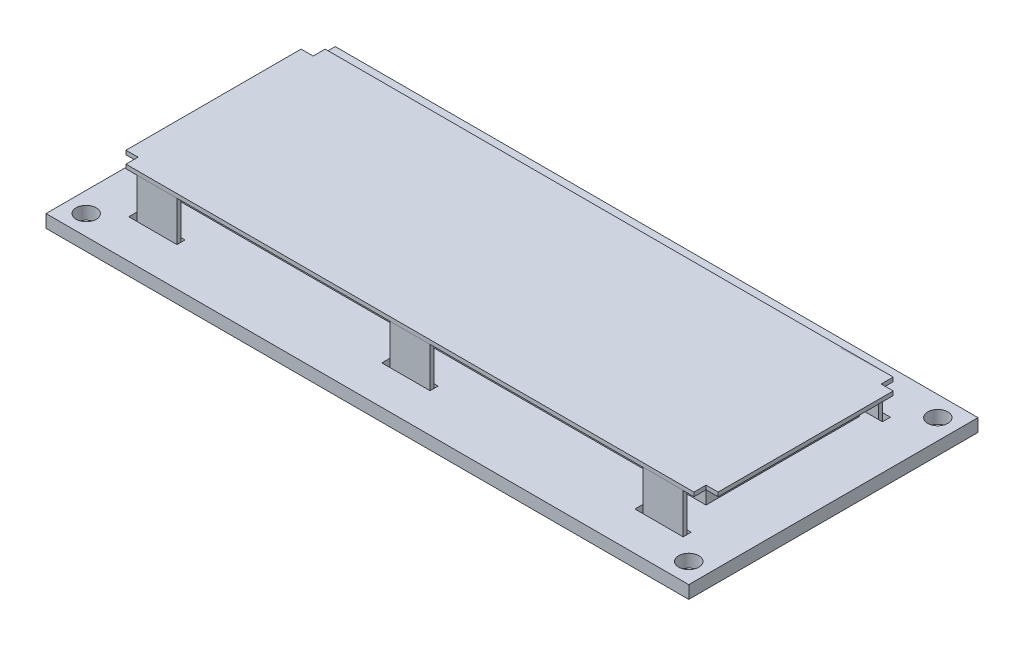
SolidWorks part; units mm, degrees
ref_plane "Ebene vorne" through (0, 0, 0) normal (0, 0, 1) x (1, 0, 0)
ref_plane "Ebene oben" through (0, 0, 0) normal (0, 1, 0) x (1, 0, 0)
ref_plane "Ebene rechts" through (0, 0, 0) normal (1, 0, 0) x (0, 0, -1)
sketch "Skizze1" plane through (0, 0, 0) normal (1, 0, 0) x (0, 0, -1)
  line L0 (0, 0) -> (36, 0)
  line L1 (0, 0) -> (0, -1.6)
  line L2 (0, -1.6) -> (36, -1.6)
  line L3 (36, -1.6) -> (36, 0)
  dimension "D1" = 36
  dimension "D2" = 1.6
extrude "Linear austragen1" add sketch "Skizze1" along normal blind 40
hole_wizard "Ø2.5 (2.5) Durchmesser Bohrung1" positions "3D-Skizze1" profile "Skizze3" hole size "Ø2.5" standard "Ansi Metrisch" end condition through all
sketch3d "3D-Skizze1"
  line L0 (40, 0, -36) -> (40, 0, 0) construction
  line L1 (40, 0, -36) -> (0, 0, -36) construction
  line L2 (40, 0, 0) -> (0, 0, 0) construction
  point P0 (37.5, 0, -2.5)
  point P2 (37.5, 0, -33.5)
  dimension "D1" = 2.5
  dimension "D2" = 2.5
  dimension "D3" = 2.5
  dimension "D4" = 2.5
sketch "Skizze3" plane through (37.5, 0, -2.5) normal (1, 0, 0) x (0, 0, 1)
  line L0 (0, 0) -> (0, 1.6)
  line L1 (0, 1.6) -> (1.25, 1.6)
  line L2 (1.25, 1.6) -> (1.25, 0)
  line L5 (1.25, 0) -> (0, 0)
  line L11 (0, -6.35) -> (0, 107.95) construction
  dimension "Bohrerdurchmesser" = 2.5
  dimension "Bohrungstiefe" = 1.6
sketch "Skizze7" plane through (0, 0, 0) normal (0, 1, 0) x (1, 0, 0)
  line L0 (0, 0) -> (0, 36) construction
  line L1 (0, 30.6) -> (3, 30.6)
  line L2 (0, 30.6) -> (0, 29.6)
  line L3 (0, 29.6) -> (3, 29.6)
  line L4 (3, 30.6) -> (3, 29.6)
  line L5 (28.5, 30.6) -> (34.5, 30.6)
  line L6 (28.5, 30.6) -> (28.5, 29.6)
  line L7 (28.5, 29.6) -> (34.5, 29.6)
  line L8 (34.5, 30.6) -> (34.5, 29.6)
  line L9 (40, 36) -> (0, 36) construction
  line L10 (40, 36) -> (40, 0) construction
  line L11 (40, 36) -> (0, 36) construction
  line L13 (34.5, 4.8) -> (34.5, 5.8)
  line L14 (28.5, 5.8) -> (34.5, 5.8)
  line L15 (28.5, 4.8) -> (28.5, 5.8)
  line L16 (28.5, 4.8) -> (34.5, 4.8)
  line L17 (3, 4.8) -> (3, 5.8)
  line L18 (0, 5.8) -> (3, 5.8)
  line L19 (0, 4.8) -> (0, 5.8)
  line L20 (0, 4.8) -> (3, 4.8)
  dimension "D1" = 1
  dimension "D2" = 5.4
  dimension "D3" = 3
  dimension "D4" = 6
  dimension "D5" = 5.5
  dimension "D6" = 25.8
extrude "Linear austragen4" cut sketch "Skizze7" against normal through all
mirror "Spiegeln1" about plane through (0, -1.6, 0) normal (1, 0, 0) of "Linear austragen4", "Linear austragen1", "Ø2.5 (2.5) Durchmesser Bohrung1"
sketch "Skizze5" plane through (0, 0, 0) normal (0, 1, 0) x (1, 0, 0)
  line L0 (0, 30.1) -> (35.35, 30.1)
  line L1 (35.35, 30.1) -> (35.35, 28.6)
  line L2 (35.35, 28.6) -> (36.85, 28.6)
  line L3 (36.85, 28.6) -> (36.85, 6.8)
  line L4 (36.85, 6.8) -> (35.35, 6.8)
  line L5 (35.35, 6.8) -> (35.35, 5.3)
  line L6 (35.35, 5.3) -> (0, 5.3)
  line L8 (0, 36) -> (0, 0) construction
  line L9 (40, 36) -> (-40, 36) construction
  line L10 (40, 36) -> (40, 0) construction
  line L11 (0, 5.3) -> (0, 30.1)
  dimension "D1" = 24.8
  dimension "D2" = 3.15
  dimension "D3" = 1.5
  dimension "D4" = 5.9
extrude "Linear austragen2" add sketch "Skizze5" along normal blind 0.5 from offset 4.5 separate body
mirror "Spiegeln8" about plane through (0, 5, -5.3) normal (1, 0, 0) of "Linear austragen2"
sketch "Skizze6" plane through (0, 5, 0) normal (0, 1, 0) x (1, 0, 0)
  line L0 (-35.35, 5.3) -> (35.35, 5.3) construction
  line L1 (35.35, 30.1) -> (-35.35, 30.1) construction
  line L2 (2.5, 30.1) -> (0, 30.1)
  line L3 (0, 30.1) -> (0, 36) construction
  line L4 (-35.35, 5.3) -> (35.35, 5.3) construction
  line L5 (0, 5.3) -> (2.5, 5.3)
  line L6 (40, 36) -> (-40, 36) construction
  line L7 (0, 30.1) -> (-2.5, 30.1)
  line L8 (0, 30.1) -> (0, 5.3) construction
  line L9 (0, 5.3) -> (-2.5, 5.3)
  line L10 (34, 30.1) -> (31.5, 30.1)
  line L12 (-2.5, 30.1) -> (-2.5, 29.6)
  line L13 (-2.5, 29.6) -> (2.5, 29.6)
  line L14 (2.5, 29.6) -> (2.5, 30.1)
  line L15 (31.5, 5.3) -> (34, 5.3)
  line L16 (31.5, 30.1) -> (29, 30.1)
  line L17 (-2.5, 5.3) -> (-2.5, 5.8)
  line L18 (-2.5, 5.8) -> (2.5, 5.8)
  line L19 (2.5, 5.8) -> (2.5, 5.3)
  line L20 (31.5, 5.3) -> (29, 5.3)
  line L21 (29, 30.1) -> (29, 29.6)
  line L22 (29, 29.6) -> (34, 29.6)
  line L23 (34, 29.6) -> (34, 30.1)
  line L24 (29, 5.3) -> (29, 5.8)
  line L25 (29, 5.8) -> (34, 5.8)
  line L26 (34, 5.8) -> (34, 5.3)
  line L27 (31.5, 30.1) -> (31.5, 5.3) construction
  line L28 (-29, 30.1) -> (-31.5, 30.1)
  line L29 (-31.5, 5.3) -> (-29, 5.3)
  line L30 (-31.5, 30.1) -> (-34, 30.1)
  line L31 (-31.5, 5.3) -> (-34, 5.3)
  line L32 (-34, 30.1) -> (-34, 29.6)
  line L33 (-34, 29.6) -> (-29, 29.6)
  line L34 (-29, 29.6) -> (-29, 30.1)
  line L35 (-34, 5.3) -> (-34, 5.8)
  line L36 (-34, 5.8) -> (-29, 5.8)
  line L37 (-29, 5.8) -> (-29, 5.3)
  line L38 (-31.5, 30.1) -> (-31.5, 36) construction
  line L39 (-31.5, 30.1) -> (-31.5, 5.3) construction
  dimension "D1" = 0.5
  dimension "D2" = 5
extrude "Linear austragen3" add sketch "Skizze6" against normal blind 11 separate body
sketch "Skizze8" plane through (0, 4.5, 0) normal (0, -1, 0) x (1, 0, 0)
  line L0 (-34, -27.25) -> (-36.85, -27.25) construction
  line L1 (-34, -27.25) -> (34, -27.25)
  line L2 (-34, -27.25) -> (-34, -8.15)
  line L3 (-34, -8.15) -> (34, -8.15)
  line L4 (34, -27.25) -> (34, -8.15)
  line L5 (-36.85, -6.8) -> (-36.85, -28.6) construction
  line L6 (-36.85, -27.25) -> (-34, -27.25) construction
  line L7 (-34, -27.25) -> (-34, -30.1) construction
  line L8 (34, -8.15) -> (34, -5.3) construction
  line L9 (29, -5.3) -> (34, -5.3) construction
  line L10 (34, -8.15) -> (36.85, -8.15) construction
  line L11 (36.85, -6.8) -> (36.85, -28.6) construction
extrude "Linear austragen5" add sketch "Skizze8" along normal blind 3
hole_wizard "Ø1.0 (1) Durchmesser Bohrung1" positions "3D-Skizze2" profile "Skizze9" hole size "Ø1.0" standard "Ansi Metrisch"
sketch3d "3D-Skizze2"
  line L0 (-40, 0, -36) -> (-40, 0, 0) construction
  line L1 (40, 0, -36) -> (-40, 0, -36) construction
  point P0 (-32, 0, -33.5)
  dimension "D1" = 8
  dimension "D2" = 2.5
sketch "Skizze9" plane through (-32, 0, -33.5) normal (1, 0, 0) x (0, 0, 1)
  line L0 (0, 0) -> (0, 1.9004)
  line L1 (0, 1.9004) -> (0.5, 1.6)
  line L2 (0.5, 1.6) -> (0.5, 0)
  line L5 (0.5, 0) -> (0, 0)
  line L10 (0, 1.9004) -> (-0.5, 1.6) construction
  line L11 (0, -6.35) -> (0, 107.95) construction
  dimension "Bohrerdurchmesser" = 1
  dimension "Bohrungstiefe" = 1.6
  dimension "Spitzenwinkel" = 118
pattern_linear "Lineares Muster1" count 16 spacing 2.54 along (1, 0, 0) of "Ø1.0 (1) Durchmesser Bohrung1"
